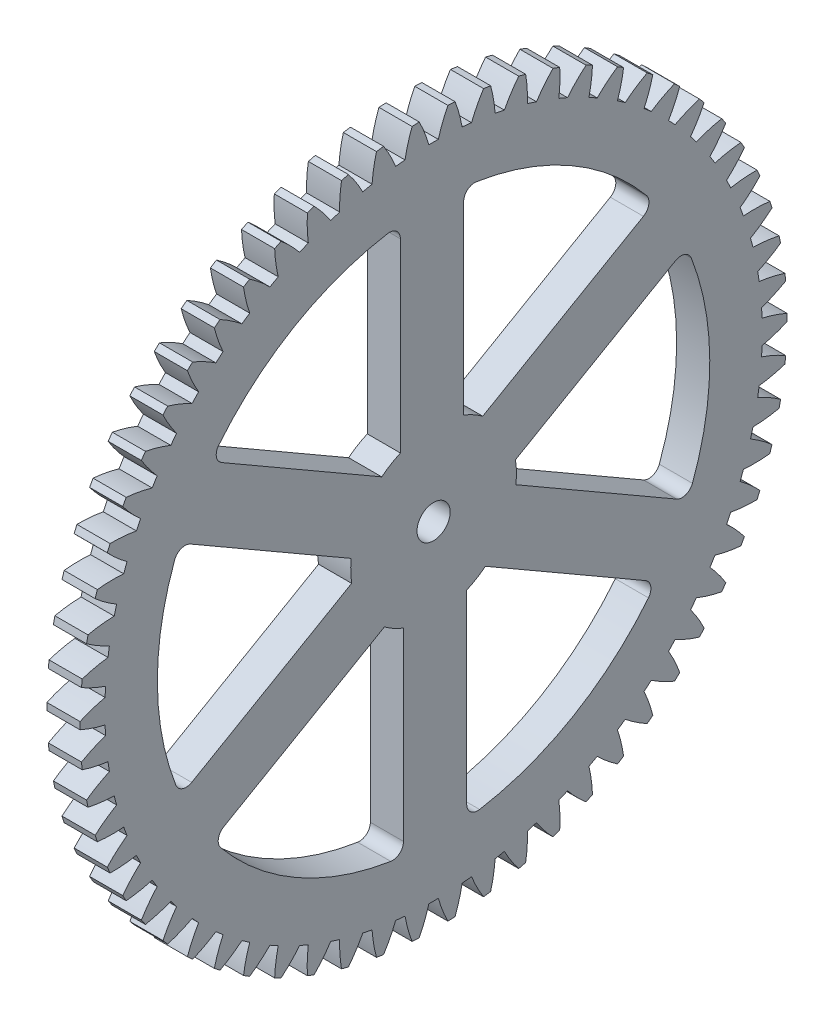
SolidWorks part; units mm, degrees
ref_plane "Plane1" through (0, 0, 0) normal (0, 0, 1) x (1, 0, 0)
ref_plane "Plane2" through (0, 0, 0) normal (0, 1, 0) x (1, 0, 0)
ref_plane "Plane3" through (0, 0, 0) normal (1, 0, 0) x (0, 0, -1)
sketch "HoldingSke" plane through (0, 0, 0) normal (0, 1, 0) x (1, 0, 0)
  line L0 (0, 0) -> (0.4695, -0.8829)
  line L1 (-15, 0) -> (100, 0) construction
  line L2 (0, 0) -> (-2.1039, 2.3779)
  line L3 (0, 0) -> (-11.863, 4.5341)
  line L4 (0, 0) -> (4.0544, 7.6251)
  line L5 (0, 0) -> (-46.8476, -17.4728)
  line L6 (0, 0) -> (-2.4869, -1.6779)
  line L7 (-2.1039, 2.3779) -> (8.6586, 51.2059)
  line L8 (-76.2, 54.61) -> (-75.7, 54.61)
  line L9 (-71.009, 38.7566) -> (-53.1078, 45.2721)
  line L10 (-76.2, 71.12) -> (104.1128, 71.12)
  line L11 (0, 0) -> (-3, 0)
  line L12 (-76.2, 101.6) -> (-76.162, 101.6)
  line L13 (24.9733, 27.94) -> (52.9518, 28.4284)
  line L14 (24.9733, 27.94) -> (24.9743, 27.94)
  line L15 (24.9733, 27.94) -> (100.4006, 29.5858)
  line L16 (-63.627, -1) -> (-12.827, -1)
  circle A0 centre (0, 0) radius 1.5
  circle A1 centre (0, 0) radius 29.749
  circle A2 centre (0, 0) radius 37.5
  circle A3 centre (0, 0) radius 1.5
  dimension "MHD" = 59.498
  dimension "Hub_dia" = 75
  dimension "Bore" = 3
  dimension "MBD" = 3
  dimension "Num_teeth" = 62
  dimension "Pitch" = 1
  dimension "Overall_len" = 50
  dimension "Show_teeth" = 62
  dimension "Thickness" = 3
  dimension "OAL" = 50.0001
  dimension "T_dim" = 0.5
  dimension "Ap" = 20
  dimension "H" = 19.05
  dimension "Pitch_radius" = 180.3128
  dimension "Width" = 3
  dimension "Backlash" = 0.038
  dimension "Addendum_fac" = 1
  dimension "Dedendum_fac" = 1.25
  dimension "Clearance_fac" = 0.25
  dimension "Dedendum_add" = 0.001
  dimension "Module" = 1
sketch "BasProSke" plane through (0, 0, 0) normal (0, 1, 0) x (1, 0, 0)
  line L0 (-10, 0) -> (60, 0) construction
  line L1 (0, 0) -> (0, 32)
  line L2 (0, 0) -> (3, 0)
  line L3 (3, 0) -> (3, 32)
  line L4 (3, 32) -> (0, 32)
  dimension "Thickness" = 3
  dimension "Diameter" = 64
revolve "Base-Revolve" add sketch "BasProSke" angle 360 about L0
sketch "TooCutSke" plane through (0, 0, 0) normal (1, 0, 0) x (0, 0, -1)
  line L1 (0, 0) -> (0, 107) construction
  line L2 (0, 0) -> (-0.8518, 30.9883) construction
  line L3 (0, 0) -> (-3.1394, 61.9038) construction
  line L4 (-0.8518, 30.9883) -> (-1.5697, 30.9519) construction
  arc A0 (0.4289, 29.7459) -> (-0.4289, 29.7459) centre (0, 0) ccw
  arc A1 (1.31, 31.9986) -> (-1.31, 31.9986) centre (0, 0) ccw
  circle A2 centre (0, 0) radius 31 construction
  circle A3 centre (0, 0) radius 29.1305 construction
  arc A4 (-0.4289, 29.7459) -> (-1.31, 31.9986) centre (-12.3625, 26.3771) ccw
  arc A5 (1.31, 31.9986) -> (0.4289, 29.7459) centre (12.3625, 26.3771) ccw
  dimension "Root_dia" = 59.498
  dimension "Overcut_dia" = 64.0508
  dimension "Pitch_dia" = 62
  dimension "Base_dia" = 58.2609
  dimension "Flank_rad" = 12.4
  dimension "Half_ang" = 2.903
  dimension "Half_CT" = 0.7188
extrude "ToothCut" cut sketch "TooCutSke" along normal through all
fillet "Breaks" [suppressed] radius 0.02
fillet "RootFillets" [suppressed] radius 0.251
pattern_circular "TeethCuts" count 62 every 5.806 about axis through (-10, 0, 0) along (1, 0, 0) of "ToothCut", "RootFillets", "Breaks"
sketch "HubNeaOneSke" plane through (0, 0, 0) normal (-1, 0, 0) x (0, 0, 1)
  circle A0 centre (0, 0) radius 29.749
  dimension "Diameter" = 59.498
extrude "HubNearOne" [suppressed] add sketch "HubNeaOneSke" along normal blind 47.0001
sketch "HubNeaBotSke" plane through (0, 0, 0) normal (-1, 0, 0) x (0, 0, 1)
  circle A0 centre (0, 0) radius 29.749
  dimension "Diameter" = 59.498
extrude "HubNearBoth" [suppressed] add sketch "HubNeaBotSke" along normal blind 23.5
ref_plane "FarPln" through (3, 0, 0) normal (1, 0, 0) x (0, 0, -1)
sketch "HubFarSke" plane through (3, 0, 0) normal (1, 0, 0) x (0, 0, -1)
  circle A0 centre (0, 0) radius 29.749
  dimension "Diameter" = 59.498
extrude "HubFar" [suppressed] add sketch "HubFarSke" along normal blind 23.5
sketch "BorSke" plane through (0, 0, 0) normal (1, 0, 0) x (0, 0, -1)
  circle A0 centre (0, 0) radius 1.5
  dimension "Diameter" = 3
extrude "Bore" cut sketch "BorSke" along normal mid plane 100.0001
sketch "KeySke" plane through (0, 0, 0) normal (1, 0, 0) x (0, 0, -1)
  line L0 (-0.6, 0) -> (-0.6, 2)
  line L1 (-0.6, 2) -> (0.6, 2)
  line L2 (0.6, 2) -> (0.6, 0)
  line L3 (0, 0) -> (0, 34) construction
  line L4 (-0.6, 0) -> (0.6, 0)
  dimension "Offset" = 2
  dimension "Width" = 1.2
extrude "Keyway" [suppressed] cut sketch "KeySke" along normal mid plane 100.0001
pattern_circular "Keyway2" [suppressed] count 2 every 90 about axis through (-10, 0, 0) along (1, 0, 0)
sketch "Sketch1" plane through (3, 0, 0) normal (1, 0, 0) x (0, 0, -1)
  line L4 (-3, 24.8193) -> (-3, 6.8739)
  line L5 (-4.6915, 5.8515) -> (-20.161, 14.7829)
  arc A4 (-3, 24.8193) -> (-20.161, 14.7829) centre (0, 0) ccw
  arc A5 (-3, 6.8739) -> (-4.6915, 5.8515) centre (0, 0) ccw
  dimension "D1" = 50
  dimension "D2" = 15
  dimension "D3" = 3
  dimension "D4" = 60
extrude "Cut-Extrude1" cut sketch "Sketch1" against normal through all
pattern_circular "CirPattern1" count 6 every 60 about axis through (0, 0, 0) along (1, 0, 0) of "Cut-Extrude1"
fillet "Fillet1" radius 1 12 edges at (1.5, -15.0077, 19.9942) (1.5, -24.8514, 2.7218) (1.5, -24.8193, -3) (1.5, -14.7829, -20.161) (1.5, -9.8116, -22.9942) (1.5, 10.0685, -22.8828) (1.5, 15.0077, -19.9942) (1.5, -10.0685, 22.8828) (1.5, 9.8116, 22.9942) (1.5, 14.7829, 20.161) (1.5, 24.8193, 3) (1.5, 24.8514, -2.7218)
equation "' \"Module@HoldingSke\" = 6.35"
equation "' \"Num_teeth@HoldingSke\" = 12"
equation "' \"Ap@HoldingSke\" =  20"
equation "' \"Ap@HoldingSke\" = 20"
equation "' \"Width@HoldingSke\" = 0.5 * 25.4"
equation "' \"Hub_dia@HoldingSke\"= 1 * 25.4"
equation "' \"Hub_dia@HoldingSke\" = 1 * 25.4"
equation "' \"Overall_len@HoldingSke\" = 1.0 * 25.4"
equation "' \"Bore@HoldingSke\" = 0.75 * 25.4"
equation "' \"T_dim@HoldingSke\" = 0.1 * 25.4"
equation "' \"Width@KeySke\" = 0.25 * 25.4"
equation "' \"Show_teeth@HoldingSke\" = 13"
equation "' \"Backlash@HoldingSke\" = 0.009 * 25.4"
equation "' \"Addendum_fac@HoldingSke\" = 1.0"
equation "' \"Dedendum_fac@HoldingSke\" = 1.25"
equation "' \"Dedendum_add@HoldingSke\" = 0.00005 * 25.4"
equation "' \"Clearance_fac@HoldingSke\" = 0.25"
equation "\"Pitch@HoldingSke\" = 1 / \"Module@HoldingSke\""
equation "\"Overcut_dia@TooCutSke\" = (\"Num_teeth@HoldingSke\" + 2 * \"Addendum_fac@HoldingSke\") / \"Pitch@HoldingSke\" + 0.002 * 25.4"
equation "\"Pitch_dia@TooCutSke\" = \"Num_teeth@HoldingSke\" / \"Pitch@HoldingSke\""
equation "\"Base_dia@TooCutSke\" = \"Num_teeth@HoldingSke\" / \"Pitch@HoldingSke\" * cos((\"Ap@HoldingSke\"  * 3.14159265 / 180))"
equation "\"Root_dia@TooCutSke\" = (\"Num_teeth@HoldingSke\" + 2) / \"Pitch@HoldingSke\" - 2 * (\"Addendum_fac@HoldingSke\" + \"Dedendum_fac@HoldingSke\") / \"Pitch@HoldingSke\" - \"Dedendum_add@HoldingSke\" * 2"
equation "\"Half_ang@TooCutSke\" = 180 / \"Num_teeth@HoldingSke\""
equation "\"Half_CT@TooCutSke\" = \"Num_teeth@HoldingSke\" / \"Pitch@HoldingSke\" * sin((3.14159265 / 2 / \"Num_teeth@HoldingSke\")) / 2 - 7 * \"Backlash@HoldingSke\" / 4"
equation "\"Flank_rad@TooCutSke\" = \"Num_teeth@HoldingSke\" / \"Pitch@HoldingSke\" / 5"
equation "\"Radius@RootFillets\" = \"Clearance_fac@HoldingSke\" / \"Pitch@HoldingSke\" + \"Dedendum_add@HoldingSke\""
equation "\"Break_rad@Breaks\" = 0.02 / \"Pitch@HoldingSke\""
equation "\"Thickness@HoldingSke\" = \"Width@HoldingSke\""
equation "\"OAL@HoldingSke\" = \"Thickness@HoldingSke\""
equation "\"MHD@HoldingSke\" = (\"Num_teeth@HoldingSke\" + 2) / \"Pitch@HoldingSke\" - 2 * (\"Addendum_fac@HoldingSke\" + \"Dedendum_fac@HoldingSke\")  / \"Pitch@HoldingSke\" - \"Dedendum_add@HoldingSke\" * 2"
equation "\"MBD@HoldingSke\" = (\"Num_teeth@HoldingSke\" + 2) / \"Pitch@HoldingSke\" - 2 * (\"Addendum_fac@HoldingSke\" + \"Dedendum_fac@HoldingSke\")  / \"Pitch@HoldingSke\" - \"Dedendum_add@HoldingSke\" * 2 - 0.002 * 25.4"
equation "\"MHD@HoldingSke\" = ((sgn( \"MHD@HoldingSke\" - \"Hub_dia@HoldingSke\" )-1)*( \"MHD@HoldingSke\" - \"Hub_dia@HoldingSke\" ))/-2+ \"Hub_dia@HoldingSke\""
equation "\"MBD@HoldingSke\" = ((sgn( \"MBD@HoldingSke\" - \"Bore@HoldingSke\" )-1)*( \"MBD@HoldingSke\" - \"Bore@HoldingSke\" ))/-2+ \"Bore@HoldingSke\""
equation "\"OAL@HoldingSke\" = ((sgn( \"OAL@HoldingSke\" - \"Overall_len@HoldingSke\" )+1)*( \"OAL@HoldingSke\" - \"Overall_len@HoldingSke\" ))/2 + \"Overall_len@HoldingSke\" + 0.000002 * 25.4"
equation "\"Num_teeth@TeethCuts\" = int( \"Show_teeth@HoldingSke\" ) + 1"
equation "\"Num_teeth@TeethCuts\" = ((sgn( \"Num_teeth@TeethCuts\" - \"Num_teeth@HoldingSke\" )-1)*( \"Num_teeth@TeethCuts\" - \"Num_teeth@HoldingSke\" ))/-2+ \"Num_teeth@HoldingSke\""
equation "\"Num_teeth@TeethCuts\" = ((sgn( \"Num_teeth@TeethCuts\" - 2.0)+1)*( \"Num_teeth@TeethCuts\" - 2.0))/2 +2.0"
equation "\"Angle@TeethCuts\" = 360.0 / \"Num_teeth@HoldingSke\""
equation "\"Diameter@BasProSke\" = (\"Num_teeth@HoldingSke\" + 2 * \"Addendum_fac@HoldingSke\") / \"Pitch@HoldingSke\""
equation "\"Thickness@BasProSke\"  = \"Thickness@HoldingSke\""
equation "' \"Fillet_rad@BasProSke\" =  \"Thickness@HoldingSke\" * 0.05"
equation "' \"Fillet_rad@BasProSke\" = \"Thickness@HoldingSke\" * 0.05"
equation "\"MHD@HoldingSke\" = ((sgn( \"MHD@HoldingSke\" - \"Root_dia@TooCutSke\" )-1)*( \"MHD@HoldingSke\" - \"Root_dia@TooCutSke\" ))/-2+ \"Root_dia@TooCutSke\""
equation "\"Diameter@HubNeaOneSke\" = \"MHD@HoldingSke\""
equation "\"Length@HubNearOne\" = \"OAL@HoldingSke\" - \"Thickness@BasProSke\""
equation "\"Diameter@HubNeaBotSke\" = \"MHD@HoldingSke\""
equation "\"Length@HubNearBoth\" = ( \"OAL@HoldingSke\" - \"Thickness@BasProSke\" ) / 2.0"
equation "\"Thickness@FarPln\" = \"Thickness@BasProSke\""
equation "\"Diameter@HubFarSke\" = \"MHD@HoldingSke\""
equation "\"Length@HubFar\" = ( \"OAL@HoldingSke\" - \"Thickness@BasProSke\" ) / 2.0"
equation "\"Diameter@BorSke\" = \"MBD@HoldingSke\""
equation "\"D1@Bore\" = \"OAL@HoldingSke\" * 2.0"
equation "\"D1@Keyway\" = \"OAL@HoldingSke\" * 2.0"
equation "\"Offset@KeySke\" = \"T_dim@HoldingSke\" + \"MBD@HoldingSke\" / 2.0"
